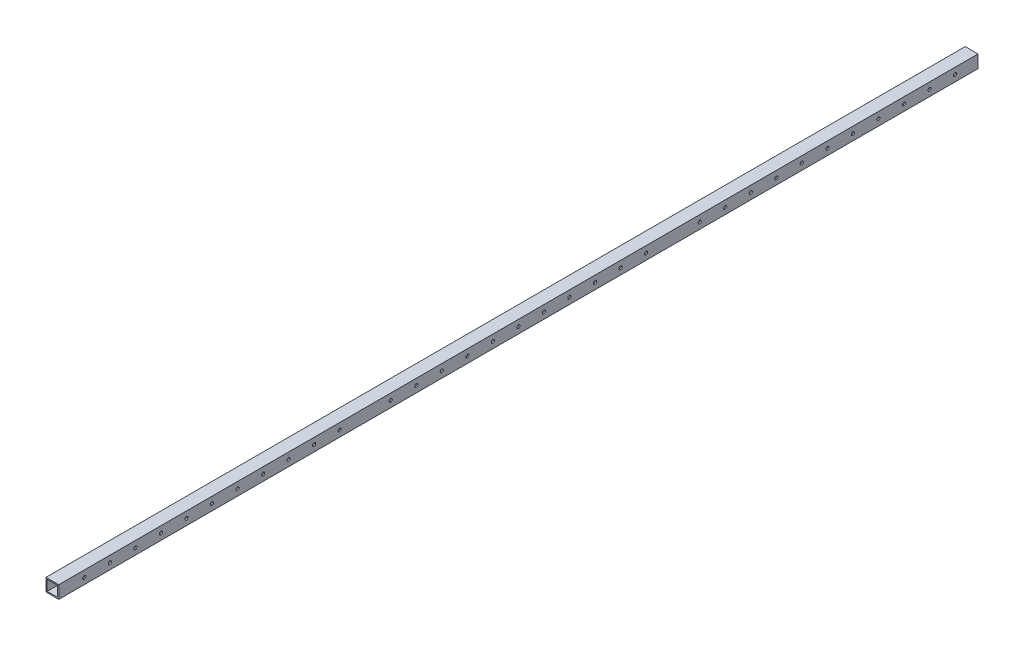
SolidWorks part; units mm, degrees
ref_plane "Front Plane" through (0, 0, 0) normal (0, 0, 1) x (1, 0, 0)
ref_plane "Top Plane" through (0, 0, 0) normal (0, 1, 0) x (1, 0, 0)
ref_plane "Right Plane" through (0, 0, 0) normal (1, 0, 0) x (0, 0, -1)
sketch "Sketch1" plane through (0, 0, 0) normal (0, 0, 1) x (1, 0, 0)
  line L0 (4.7625, 4.7625) -> (4.7625, 46.0375)
  line L1 (0, 0) -> (50.8, 0)
  line L2 (0, 0) -> (0, 50.8)
  line L3 (0, 50.8) -> (50.8, 50.8)
  line L4 (50.8, 0) -> (50.8, 50.8)
  line L5 (4.7625, 46.0375) -> (46.0375, 46.0375)
  line L6 (46.0375, 4.7625) -> (46.0375, 46.0375)
  line L7 (4.7625, 4.7625) -> (46.0375, 4.7625)
  dimension "D1" = 50.8
  dimension "D2" = 4.7625
extrude "Boss-Extrude1" add sketch "Sketch1" along normal blind 3657.6
sketch "Sketch2" plane through (0, 0, 0) normal (-1, 0, 0) x (0, 0, 1)
  line L0 (3657.6, 50.8) -> (3657.6, 0) construction
  line L1 (3657.6, 50.8) -> (0, 50.8) construction
  circle A0 centre (3556, 25.4) radius 6.35
  dimension "D1" = 12.7
  dimension "D2" = 101.6
  dimension "D3" = 25.4
extrude "Cut-Extrude1" cut sketch "Sketch2" against normal through all both and the other way through all
pattern_linear "LPattern1" count 11 spacing 101.6 along (0, 0, -1) of "Cut-Extrude1"
sketch "Sketch3" plane through (0, 0, 0) normal (-1, 0, 0) x (0, 0, 1)
  line L0 (3657.6, 0) -> (0, 0) construction
  circle A0 centre (2336.8, 25.4) radius 6.35
  circle A1 centre (2540, 25.4) radius 6.35 construction
  dimension "D1" = 12.7
  dimension "D2" = 203.2
  dimension "D3" = 25.4
extrude "Cut-Extrude2" cut sketch "Sketch3" against normal through all
pattern_linear "LPattern2" count 11 spacing 101.6 along (0, 0, -1) of "Cut-Extrude2"
sketch "Sketch4" plane through (0, 0, 0) normal (-1, 0, 0) x (0, 0, 1)
  line L0 (3657.6, 0) -> (0, 0) construction
  circle A0 centre (1107.44, 25.4) radius 6.35
  circle A1 centre (1320.8, 25.4) radius 6.35 construction
  dimension "D2" = 12.7
  dimension "D1" = 25.4
  dimension "D3" = 213.36
extrude "Cut-Extrude3" cut sketch "Sketch4" against normal through all
pattern_linear "LPattern3" count 11 spacing 101.6 along (0, 0, -1) of "Cut-Extrude3"
